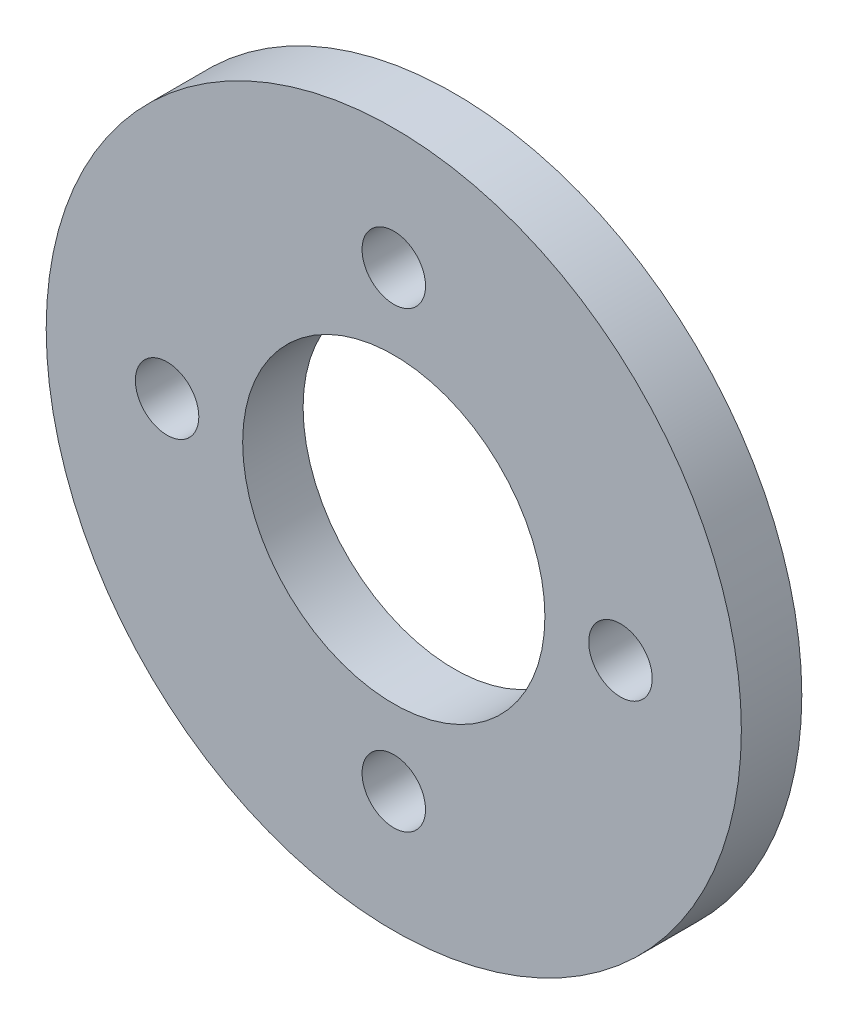
SolidWorks part; units mm, degrees
ref_plane "Front Plane" through (0, 0, 0) normal (0, 0, 1) x (1, 0, 0)
ref_plane "Top Plane" through (0, 0, 0) normal (0, 1, 0) x (1, 0, 0)
ref_plane "Right Plane" through (0, 0, 0) normal (1, 0, 0) x (0, 0, -1)
sketch "Sketch1" plane through (0, 0, 0) normal (0, 0, 1) x (1, 0, 0)
  circle A0 centre (0, 0) radius 23
  circle A1 centre (0, 15) radius 2.1
  circle A2 centre (15, 0) radius 2.1
  circle A3 centre (0, -15) radius 2.1
  circle A4 centre (-15, 0) radius 2.1
  circle A5 centre (0, 0) radius 10
  point P14 (0, 0)
  dimension "D1" = 46
  dimension "D2" = 4.2
  dimension "D5" = 20
  dimension "D3" = 15
  dimension "D4" = 4
extrude "Boss-Extrude1" add sketch "Sketch1" along normal blind 4
